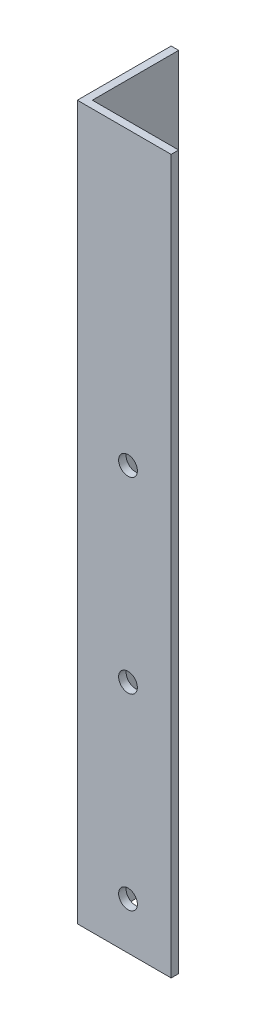
SolidWorks part; units mm, degrees
ref_plane "Спереди" through (0, 0, 0) normal (0, 0, 1) x (1, 0, 0)
ref_plane "Сверху" through (0, 0, 0) normal (0, 1, 0) x (1, 0, 0)
ref_plane "Справа" through (0, 0, 0) normal (1, 0, 0) x (0, 0, -1)
sketch "Эскиз1" plane through (0, 0, 0) normal (0, 1, 0) x (1, 0, 0)
  line L0 (0, 0) -> (50, 0)
  line L1 (0, 0) -> (0, 50)
extrude "Вытянуть-Тонкостенный1" add sketch "Эскиз1" along normal blind 380 thin thin type one direction wall 4
sketch "Эскиз2" plane through (0, 0, 0) normal (0, 0, 1) x (1, 0, 0)
  circle A0 centre (27, 225) radius 5
  circle A1 centre (27, 125) radius 5
  circle A2 centre (27, 25) radius 5
  dimension "D1" = 3
extrude "Вырез-Вытянуть1" cut sketch "Эскиз2" against normal blind 10
sketch "Эскиз3" plane through (0, 0, 0) normal (-1, 0, 0) x (0, 0, 1)
  circle A0 centre (-23, 225) radius 5
  circle A1 centre (-23, 125) radius 5
  circle A2 centre (-23, 25) radius 5
  dimension "D1" = 3
extrude "Вырез-Вытянуть2" cut sketch "Эскиз3" against normal blind 10
